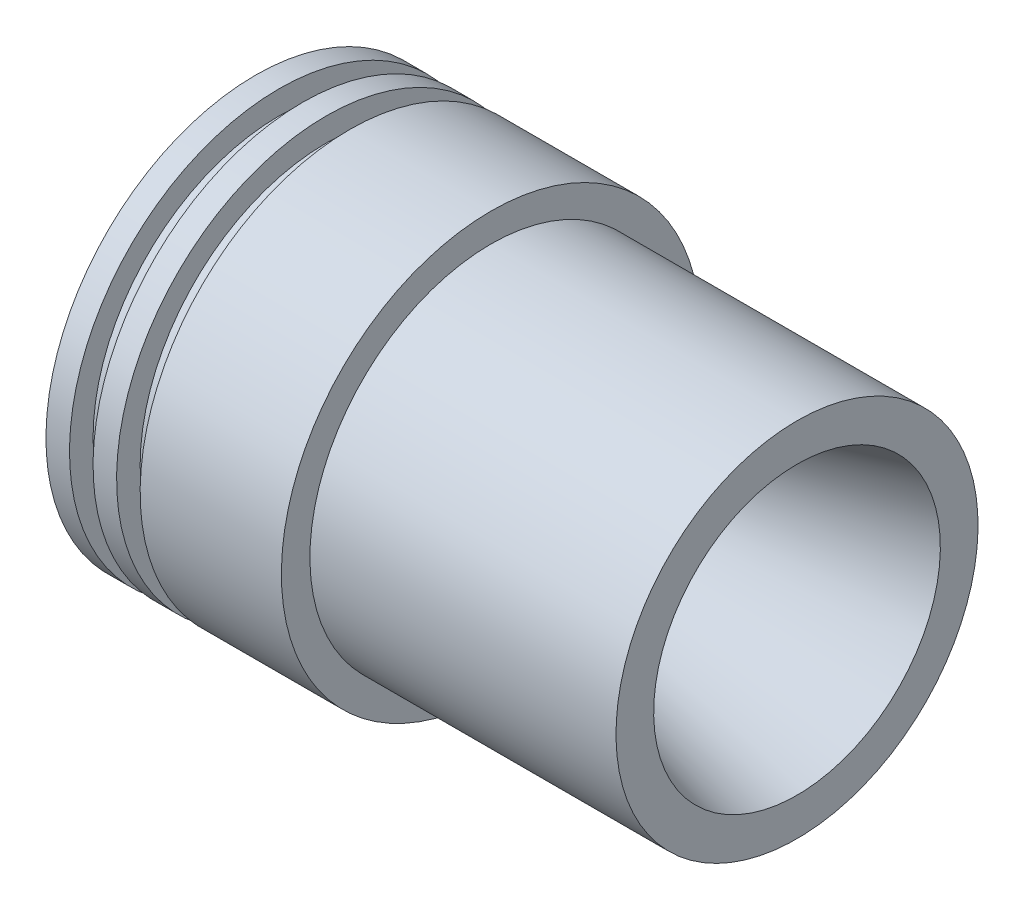
SolidWorks part; units mm, degrees
material "AISI 4130 Steel, annealed at 865C"
ref_plane "Front Plane" through (0, 0, 0) normal (0, 0, 1) x (1, 0, 0)
ref_plane "Top Plane" through (0, 0, 0) normal (0, 1, 0) x (1, 0, 0)
ref_plane "Right Plane" through (0, 0, 0) normal (1, 0, 0) x (0, 0, -1)
sketch "Sketch1" plane through (0, 0, 0) normal (0, 0, 1) x (1, 0, 0)
  line L0 (0, 0) -> (-115, 0) construction
  line L24 (-115, 36.5) -> (-71.6987, 11.5)
  line L25 (-71.6987, 11.5) -> (-70.6987, 11.5)
  line L26 (-70.6987, 11.5) -> (0, 30.4437)
  line L27 (-115, 36.5) -> (-115, 44.5)
  line L28 (-115, 44.5) -> (-110, 44.5)
  line L29 (-110, 44.5) -> (-110, 39.5)
  line L30 (-110, 39.5) -> (-105, 39.5)
  line L31 (-105, 39.5) -> (-105, 44.5)
  line L32 (-105, 44.5) -> (-100, 44.5)
  line L33 (-100, 44.5) -> (-100, 39.5)
  line L34 (-100, 39.5) -> (-95, 39.5)
  line L35 (-95, 39.5) -> (-95, 44.5)
  line L36 (0, 30.4437) -> (0, 38.4437)
  line L38 (-95, 44.5) -> (-65, 44.5)
  line L39 (0, 38.4437) -> (-65, 38.4437)
  line L40 (-65, 38.4437) -> (-65, 44.5)
  dimension "D1" = 115
  dimension "D2" = 73
  dimension "D3" = 30
  dimension "D4" = 1
  dimension "D5" = 15
  dimension "D6" = 23
  dimension "D7" = 8
  dimension "D8" = 5
  dimension "D9" = 5
  dimension "D10" = 5
  dimension "D11" = 5
  dimension "D12" = 5
  dimension "D13" = 50
  dimension "D14" = 8
revolve "Revolve1" add sketch "Sketch1" angle 360 about L0
